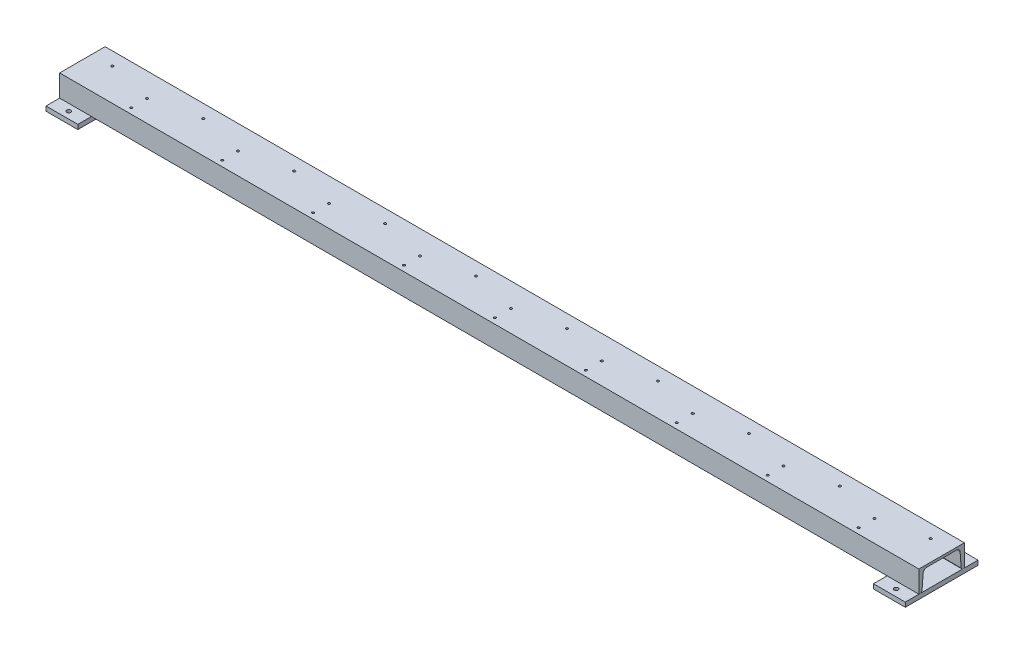
SolidWorks part; units mm, degrees
material "A3钢"
ref_plane "前视基准面" through (0, 0, 0) normal (0, 0, 1) x (1, 0, 0)
ref_plane "上视基准面" through (0, 0, 0) normal (0, 1, 0) x (1, 0, 0)
ref_plane "右视基准面" through (0, 0, 0) normal (1, 0, 0) x (0, 0, -1)
sketch "草图1" plane through (0, 0, 0) normal (0, 0, 1) x (1, 0, 0)
  line L0 (0, 659.1652) -> (0, -626.1553) construction
  line L1 (-1071.9945, 0) -> (1309.6653, 0) construction
  line L2 (-945, 0) -> (945, 0)
  line L3 (-945, -150) -> (945, -150)
  line L4 (945, -150) -> (945, 0)
  line L5 (-945, 0) -> (-945, -150)
  dimension "D1" = 1890
  dimension "D2" = 150
other "槽钢 10(1)"
ref_plane "基准面1" through (-945, 0, 0) normal (1, 0, 0) x (0, 1, 0)
sketch "Sketch1" plane through (-945, 0, 0) normal (1, 0, 0) x (0, 1, 0)
  line L0 (0, 0) -> (0, -100)
  line L1 (0, -100) -> (-48, -100)
  line L2 (0, -50) -> (-5.3, -50) construction
  line L3 (-5.3, -82.1991) -> (-5.3, -17.8009)
  line L4 (-13.1549, -90.6746) -> (-44.0725, -93.0278)
  line L5 (-48, -97.2655) -> (-48, -100)
  line L6 (-5.3, -90.0767) -> (-5.3, -93.3267) construction
  line L7 (-5.3, -93.3267) -> (-48, -93.3267) construction
  line L8 (-24, -100) -> (-24, -91.5) construction
  line L9 (-48, -2.7345) -> (-48, 0)
  line L10 (0, 0) -> (-48, 0)
  line L11 (-13.1549, -9.3254) -> (-44.0725, -6.9722)
  arc A0 (-5.3, -82.1991) -> (-13.1549, -90.6746) centre (-13.8, -82.1991) cw
  arc A1 (-13.1549, -9.3254) -> (-5.3, -17.8009) centre (-13.8, -17.8009) cw
  arc A2 (-44.0725, -93.0278) -> (-48, -97.2655) centre (-43.75, -97.2655) ccw
  arc A3 (-48, -2.7345) -> (-44.0725, -6.9722) centre (-43.75, -2.7345) ccw
  point P2 (-24, 0)
  point P17 (0, 0)
  point P20 (-5.3, -9.9233)
  point P26 (-48, -6.6733)
  dimension "r" = 8.5
  dimension "r1" = 4.25
  dimension "h" = 100
  dimension "b" = 48
  dimension "d" = 5.3
  dimension "t" = 8.5
  dimension "D5" = 42.7
  dimension "D6" = 3.25
sketch "草图8" plane through (0, 0, 0) normal (0, 1, 0) x (1, 0, 0)
  line L0 (-780.539, 30) -> (-934.4979, 30) construction
  line L1 (945, 0) -> (-945, 0) construction
  line L2 (-800, 12.5) -> (-800, 47.5) construction
  line L3 (-945, 100) -> (-945, 0) construction
  dimension "D1" = 30
  dimension "D2" = 145
  dimension "D3" = 35
hole_wizard "M6 螺纹孔1" positions "3D草图2" profile "草图9" tap size "M6" standard "GB" end condition through all
sketch3d "3D草图2"
  point P0 (-800, 0, -12.5)
  point P3 (-800, 0, -47.5)
sketch "草图9" plane through (-800, 0, -12.5) normal (1, 0, 0) x (0, 0, 1)
  line L0 (0, 0) -> (0, 48)
  line L1 (0, 48) -> (2.5, 48)
  line L2 (2.5, 48) -> (2.5, 0)
  line L5 (2.5, 0) -> (0, 0)
  line L11 (0, -6.35) -> (0, 107.95) construction
  dimension "通孔螺纹孔钻头直径" = 5
  dimension "通孔螺纹孔钻头深度" = 48
cosmetic thread "孔螺蚊线1" parameters "D2"=6
cosmetic thread "孔螺蚊线2" parameters "D2"=6
pattern_linear "阵列(线性)2" count 9 spacing 200 along (1, 0, 0) of "M6 螺纹孔1"
sketch "草图10" plane through (0, -48, 0) normal (0, -1, 0) x (1, 0, 0)
  line L0 (-945, 0) -> (-945, -2.7345) construction
  line L1 (-875, -130) -> (-945, -130)
  line L2 (-875, -130) -> (-875, 30)
  line L3 (-875, 30) -> (-945, 30)
  line L4 (-945, -130) -> (-945, 30)
  line L5 (-875, -130) -> (-945, 30) construction
  line L6 (-875, 30) -> (-945, -130) construction
  line L7 (-945, -50) -> (-749.9105, -50) construction
  line L8 (945, 0) -> (-945, 0) construction
  line L9 (945, -100) -> (-945, -100) construction
  point P0 (-910, -50)
  dimension "D1" = 160
  dimension "D2" = 70
extrude "凸台-拉伸1" add sketch "草图10" along normal blind 10 separate body
sketch "草图11" plane through (0, -48, 0) normal (0, 1, 0) x (1, 0, 0)
  line L0 (-910, 130) -> (-910, -30) construction
  line L1 (-945, 130) -> (-875, 130) construction
  line L2 (-875, -30) -> (-945, -30) construction
  line L3 (-945, 50) -> (-718.0008, 50) construction
  line L4 (-945, 100) -> (-945, 0) construction
  line L5 (-910, 115) -> (-910, -15) construction
  dimension "D1" = 130
hole_wizard "Ø9.0 (9) 直径孔1" positions "3D草图3" profile "草图13" hole size "Ø9.0" standard "GB" end condition through all
sketch3d "3D草图3"
  point P0 (-910, -48, -115)
  point P3 (-910, -48, 15)
sketch "草图13" plane through (-910, -48, -115) normal (1, 0, 0) x (0, 0, 1)
  line L0 (0, 0) -> (0, 10)
  line L1 (0, 10) -> (4.5, 10)
  line L2 (4.5, 10) -> (4.5, 0)
  line L5 (4.5, 0) -> (0, 0)
  line L11 (0, -6.35) -> (0, 107.95) construction
  dimension "通孔孔直径" = 9
  dimension "通孔孔深度" = 10
mirror "镜向1" about plane through (0, 0, 0) normal (1, 0, 0) of bodies 121
sketch "草图14" plane through (0, 0, 0) normal (0, 1, 0) x (1, 0, 0)
  line L0 (0, 0) -> (0, 291.3204) construction
  line L1 (900, 71) -> (701.2766, 71) construction
  line L2 (945, 100) -> (945, 0) construction
  line L3 (945, 100) -> (-945, 100) construction
  dimension "D1" = 45
  dimension "D2" = 29
hole_wizard "M6 螺纹孔2" positions "3D草图4" profile "草图15" tap size "M6" standard "GB" end condition up to next
sketch3d "3D草图4"
  point P0 (900, 0, -71)
sketch "草图15" plane through (900, 0, -71) normal (1, 0, 0) x (0, 0, 1)
  line L0 (0, 0) -> (0, 5.301)
  line L1 (0, 5.301) -> (2.5, 5.301)
  line L2 (2.5, 5.301) -> (2.5, 0)
  line L5 (2.5, 0) -> (0, 0)
  line L11 (0, -6.35) -> (0, 107.95) construction
  dimension "通孔螺纹孔钻头直径" = 5
  dimension "通孔螺纹孔钻头深度" = 5.301
cosmetic thread "孔螺蚊线3" parameters "D2"=6
pattern_linear "阵列(线性)3" count 10 spacing 200 along (-1, 0, 0) of "M6 螺纹孔2"
